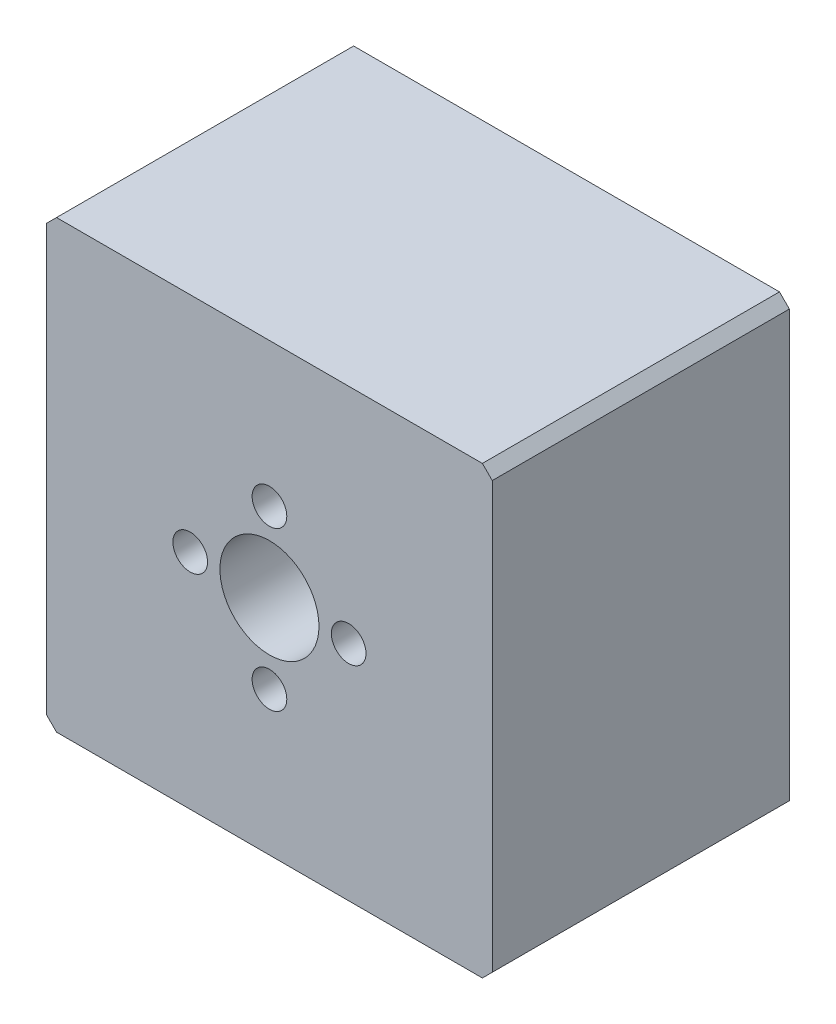
SolidWorks part; units mm, degrees
ref_plane "Front Plane" through (0, 0, 0) normal (0, 0, 1) x (1, 0, 0)
ref_plane "Top Plane" through (0, 0, 0) normal (0, 1, 0) x (1, 0, 0)
ref_plane "Right Plane" through (0, 0, 0) normal (1, 0, 0) x (0, 0, -1)
sketch "Sketch1" plane through (0, 0, 0) normal (0, 0, 1) x (1, 0, 0)
  line L0 (-22.5, 20) -> (22.5, 20)
  line L1 (22.5, 20) -> (22.5, -25)
  line L2 (22.5, -25) -> (-22.5, -25)
  line L3 (-22.5, -25) -> (-22.5, 20)
  circle A0 centre (0, -2.5) radius 5
extrude "Boss-Extrude1" add sketch "Sketch1" along normal mid plane 30
sketch "Sketch2" plane through (0, 0, 15) normal (0, 0, 1) x (1, 0, 0)
  circle A1 centre (0, 5.5) radius 1.75
  circle A2 centre (0, -10.5) radius 1.75
  circle A3 centre (8, -2.5) radius 1.75
  circle A4 centre (-8, -2.5) radius 1.75
extrude "Cut-Extrude1" cut sketch "Sketch2" against normal blind 10
chamfer "Chamfer1" distance 1 angle 45 4 edges at (-22.5, -25, 0) (22.5, -25, 0) (-22.5, 20, 0) (22.5, 20, 0)
sketch "Sketch3" plane through (0, -25, 0) normal (0, -1, 0) x (1, 0, 0)
  line L0 (24.75, 0) -> (-24.75, 0) construction
  line L1 (0, -16.5) -> (0, 16.5) construction
  circle A0 centre (-15, 8) radius 2
  circle A1 centre (15, 8) radius 2
  circle A2 centre (15, -8) radius 2
  circle A3 centre (-15, -8) radius 2
  dimension "D1" = 4
  dimension "D2" = 4
  dimension "D3" = 4
  dimension "D4" = 4
  dimension "D5" = 16
  dimension "D6" = 16
  dimension "D7" = 8
  dimension "D8" = 8
  dimension "D9" = 30
  dimension "D10" = 8
  dimension "D11" = 30
  dimension "D12" = 15
extrude "Cut-Extrude2" cut sketch "Sketch3" against normal blind 10
